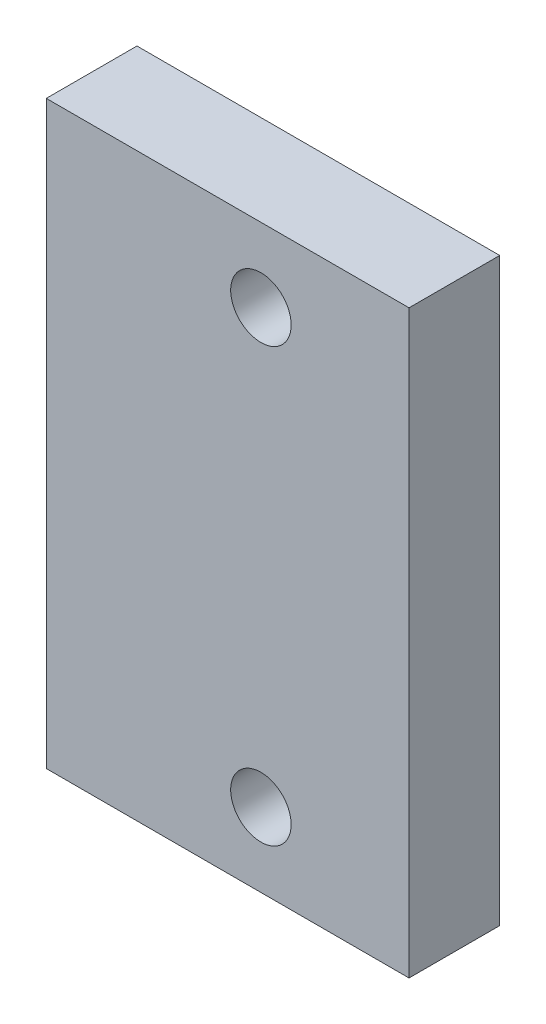
SolidWorks part; units mm, degrees
material "Balsa"
ref_plane "Front Plane" through (0, 0, 0) normal (0, 0, 1) x (1, 0, 0)
ref_plane "Top Plane" through (0, 0, 0) normal (0, 1, 0) x (1, 0, 0)
ref_plane "Right Plane" through (0, 0, 0) normal (1, 0, 0) x (0, 0, -1)
sketch "Sketch1" plane through (0, 0, 0) normal (0, 0, 1) x (1, 0, 0)
  line L0 (-15, 316.5094) -> (60, 316.5094) construction
  line L1 (0, 220.5094) -> (60, 220.5094)
  line L2 (0, 220.5094) -> (0, 316.5094)
  line L3 (0, 316.5094) -> (60, 316.5094)
  line L4 (60, 220.5094) -> (60, 316.5094)
  circle A0 centre (35.5, 232.7289) radius 5
  circle A1 centre (35.5, 304.2898) radius 5
  dimension "D1" = 60
extrude "Boss-Extrude1" add sketch "Sketch1" along normal blind 15
